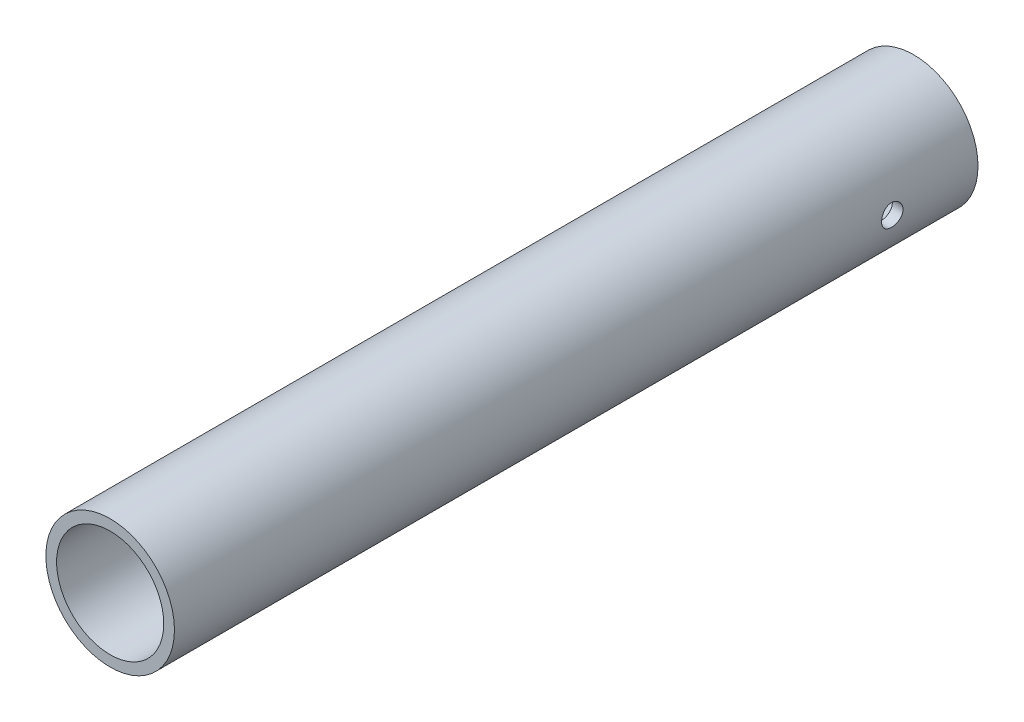
SolidWorks part; units mm, degrees
ref_plane "Ön Düzlem" through (0, 0, 0) normal (0, 0, 1) x (1, 0, 0)
ref_plane "Üst Düzlem" through (0, 0, 0) normal (0, 1, 0) x (1, 0, 0)
ref_plane "Sağ Düzlem" through (0, 0, 0) normal (1, 0, 0) x (0, 0, -1)
sketch "Sketch1" plane through (0, 0, 0) normal (0, 0, 1) x (1, 0, 0)
  circle A0 centre (0, 0) radius 6
  circle A1 centre (0, 0) radius 5
  dimension "D1" = 10
  dimension "D2" = 1
extrude "Boss-Extrude1" add sketch "Sketch1" along normal blind 75
sketch "Çizim1" plane through (0, 0, 0) normal (1, 0, 0) x (0, 0, -1)
  line L0 (0, -6) -> (0, 6) construction
  circle A0 centre (-8, 0) radius 1
  dimension "D1" = 2
  dimension "D2" = 8
extrude "Kes-Ekstrüzyon1" cut sketch "Çizim1" against normal through all both and the other way through all
